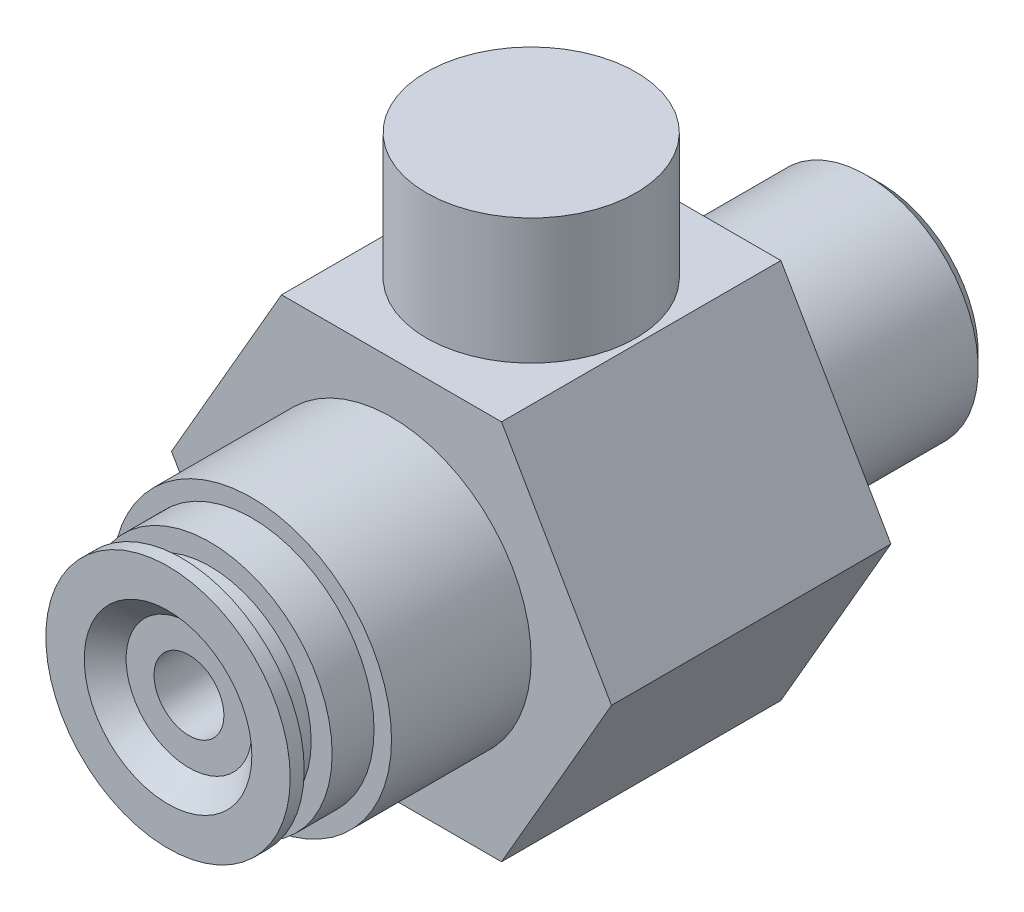
SolidWorks part; units mm, degrees
material "Aluminum Bronze"
ref_plane "Front Plane" through (0, 0, 0) normal (0, 0, 1) x (1, 0, 0)
ref_plane "Top Plane" through (0, 0, 0) normal (0, 1, 0) x (1, 0, 0)
ref_plane "Right Plane" through (0, 0, 0) normal (1, 0, 0) x (0, 0, -1)
sketch "Sketch1" plane through (0, 0, 0) normal (0, 0, 1) x (1, 0, 0)
  line L0 (-7.875, 13.6399) -> (7.875, 13.6399)
  line L1 (7.875, 13.6399) -> (15.75, 0)
  line L2 (15.75, 0) -> (7.875, -13.6399)
  line L3 (7.875, -13.6399) -> (-7.875, -13.6399)
  line L4 (-7.875, -13.6399) -> (-15.75, 0)
  line L5 (-15.75, 0) -> (-7.875, 13.6399)
  line L6 (-21.5125, 0) -> (24.1319, 0) construction
  line L7 (0, 0) -> (-10.4268, 18.0598) construction
  line L8 (0, 0) -> (12.1373, -21.0225) construction
  line L9 (0, 0) -> (11.9756, 20.7424) construction
  line L10 (0, 0) -> (-12.7407, -22.0676) construction
  circle A0 centre (0, 0) radius 15.75 construction
  dimension "D1" = 31.5
  dimension "D2" = 60
  dimension "D3" = 60
extrude "Boss-Extrude1" add sketch "Sketch1" along normal blind 20
sketch "Sketch2" plane through (0, 0, 20) normal (0, 0, 1) x (1, 0, 0)
  circle A0 centre (0, 0) radius 10
  dimension "D1" = 20
extrude "Boss-Extrude2" add sketch "Sketch2" along normal blind 10
sketch "Sketch3" plane through (0, 0, 30) normal (0, 0, 1) x (1, 0, 0)
  circle A0 centre (0, 0) radius 8.75
  dimension "D1" = 17.5
extrude "Boss-Extrude3" add sketch "Sketch3" along normal blind 6
sketch "Sketch4" plane through (0, 0, 0) normal (0, 1, 0) x (1, 0, 0)
  line L0 (0, -45.2545) -> (0, -21.2162) construction
  line L1 (0, -36) -> (-6, -36)
  line L2 (-8.75, -36) -> (8.75, -36) construction
  line L3 (-6, -36) -> (-4.5, -34.5)
  line L4 (-4.5, -34.5) -> (0, -34.5)
  line L5 (0, -34.5) -> (0, -36)
  dimension "D1" = 1.5
  dimension "D2" = 1.5
  dimension "D3" = 4.5
revolve "Cut-Revolve1" cut sketch "Sketch4" angle 360 about L0
sketch "Sketch5" plane through (0, 0, 34.5) normal (0, 0, 1) x (1, 0, 0)
  circle A0 centre (0, 0) radius 2.5
  dimension "D1" = 5
extrude "Cut-Extrude1" cut sketch "Sketch5" against normal blind 18.5
sketch "Sketch6" plane through (0, 0, 0) normal (0, 1, 0) x (1, 0, 0)
  line L0 (0, -40.6573) -> (0, -30.4272) construction
  line L1 (-8.75, -35) -> (-7.25, -35)
  line L2 (-8.75, -30) -> (-8.75, -36) construction
  line L3 (-7.25, -35) -> (-7.25, -33)
  line L4 (-7.25, -33) -> (-8.75, -33)
  line L5 (-8.75, -33) -> (-8.75, -35)
  line L6 (-8.75, -36) -> (8.75, -36) construction
  dimension "D1" = 1
  dimension "D2" = 2
  dimension "D3" = 1.5
revolve "Cut-Revolve2" cut sketch "Sketch6" angle 360 about L0
sketch "Sketch7" plane through (0, -13.6399, 0) normal (0, -1, 0) x (1, 0, 0)
  line L0 (0, -12.2286) -> (0, 27.4831) construction
  line L1 (-28.3933, 10) -> (29.5544, 10) construction
  line L2 (-7.875, 20) -> (7.875, 20) construction
  circle A0 centre (0, 10) radius 4
  dimension "D2" = 8
  dimension "D1" = 10
extrude "Boss-Extrude4" add sketch "Sketch7" along normal blind 4
sketch "Sketch8" plane through (0, -17.6399, 0) normal (0, -1, 0) x (1, 0, 0)
  line L0 (-3, 7.3542) -> (-3, 12.6458)
  line L1 (3, 7.3542) -> (3, 12.6458)
  line L2 (0, 17.7214) -> (0, 3.2188) construction
  circle A0 centre (0, 10) radius 4
  circle M4 centre (0, 10) radius 4
  dimension "D1" = 3
  dimension "D2" = 3
extrude "Cut-Extrude2" cut sketch "Sketch8" against normal blind 4 contours L0 M4 | L1 M4
sketch "Sketch9" plane through (0, 13.6399, 0) normal (0, 1, 0) x (1, 0, 0)
  line L0 (0, 12.3864) -> (0, -27.9029) construction
  line L1 (-29.4592, -10) -> (34.4766, -10) construction
  line L2 (7.875, 0) -> (-7.875, 0) construction
  circle A0 centre (0, -10) radius 7.5
  dimension "D2" = 15
  dimension "D1" = 10
extrude "Boss-Extrude5" add sketch "Sketch9" along normal blind 9
sketch "Sketch10" plane through (0, 0, 0) normal (0, 0, -1) x (-1, 0, 0)
  circle A0 centre (0, 0) radius 8
  circle A1 centre (0, 0) radius 5
  dimension "D1" = 16
  dimension "D2" = 3
extrude "Boss-Extrude6" add sketch "Sketch10" along normal blind 15
chamfer "Chamfer1" distance 1 angle 45 1 edges at (-8, 0, -15)
